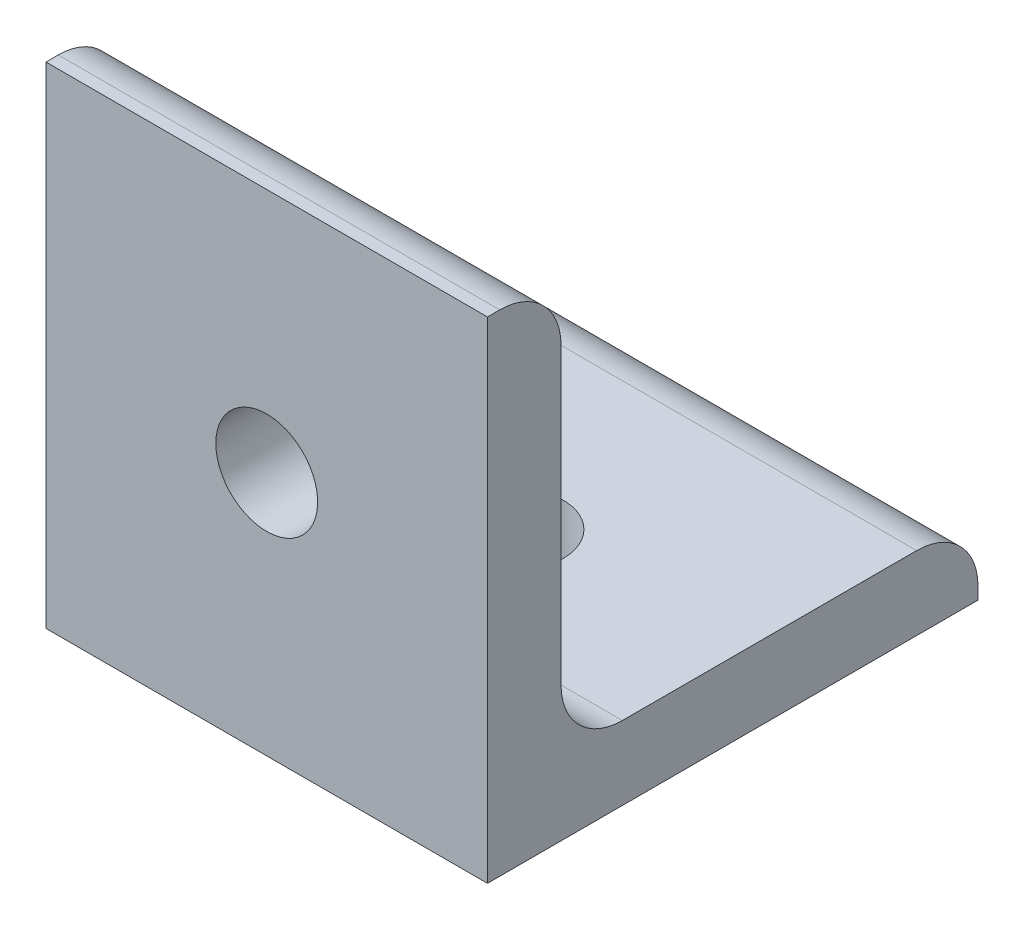
SolidWorks part; units mm, degrees
ref_plane "Front Plane" through (0, 0, 0) normal (0, 0, 1) x (1, 0, 0)
ref_plane "Top Plane" through (0, 0, 0) normal (0, 1, 0) x (1, 0, 0)
ref_plane "Right Plane" through (0, 0, 0) normal (1, 0, 0) x (0, 0, -1)
sketch "Sketch1" plane through (0, 0, 0) normal (1, 0, 0) x (0, 0, -1)
  line L0 (0, 40) -> (0, 0)
  line L1 (0, 0) -> (40, 0)
  line L2 (6, 40) -> (6, 6)
  line L3 (6, 6) -> (40, 6)
  line L4 (0, 40) -> (6, 40)
  line L5 (40, 6) -> (40, 0)
  dimension "D1" = 40
  dimension "D2" = 6
extrude "Boss-Extrude1" add sketch "Sketch1" along normal mid plane 36
sketch "Sketch2" plane through (0, 6, 0) normal (0, 1, 0) x (1, 0, 0)
  circle A0 centre (0, 20) radius 4.15
  dimension "D1" = 8.3
  dimension "D2" = 20
extrude "Cut-Extrude1" cut sketch "Sketch2" against normal through all contours A0
sketch "Sketch3" plane through (0, 0, -6) normal (0, 0, -1) x (-1, 0, 0)
  circle A0 centre (0, 20) radius 4.15
  dimension "D1" = 8.3
  dimension "D2" = 20
extrude "Cut-Extrude2" cut sketch "Sketch3" against normal through all
fillet "Fillet1" radius 5 3 edges at (0, 40, -6) (0, 6, -40) (0, 6, -6)
